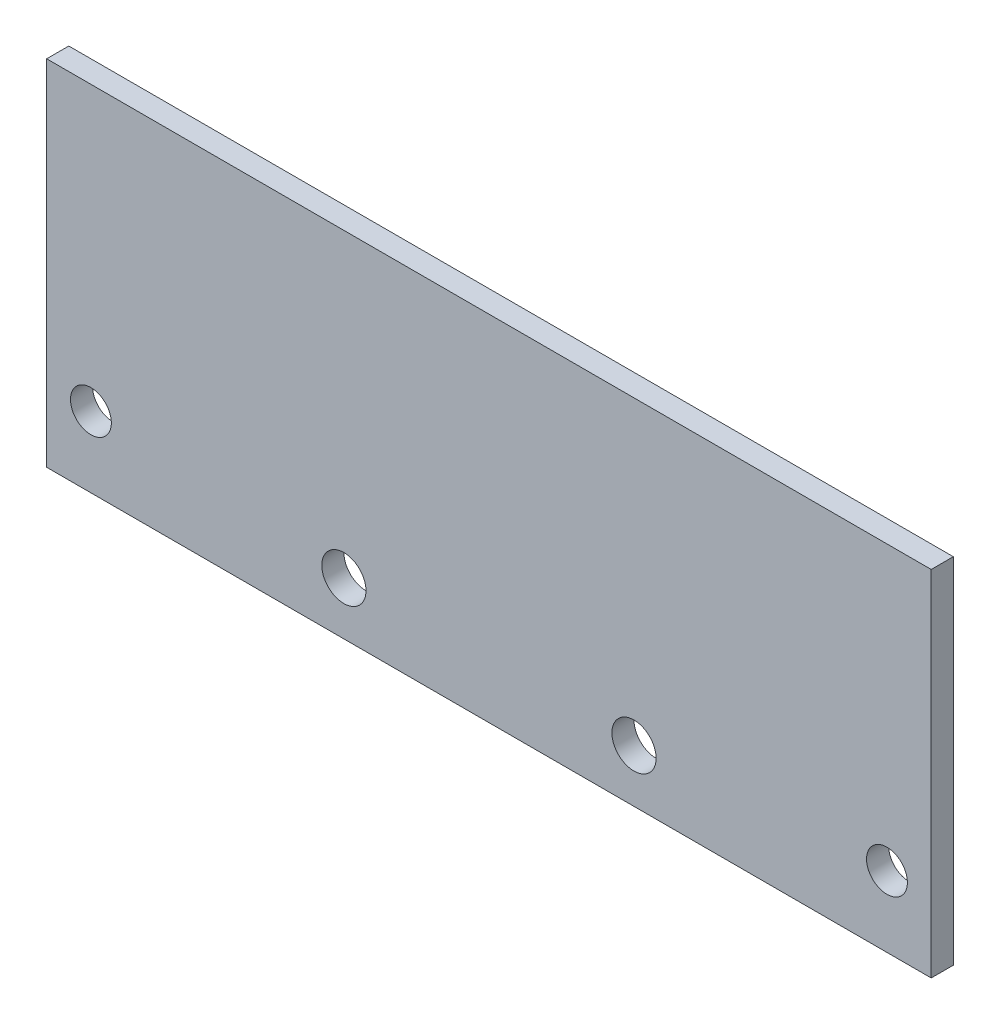
SolidWorks part; units mm, degrees
ref_plane "Front Plane" through (0, 0, 0) normal (0, 0, 1) x (1, 0, 0)
ref_plane "Top Plane" through (0, 0, 0) normal (0, 1, 0) x (1, 0, 0)
ref_plane "Right Plane" through (0, 0, 0) normal (1, 0, 0) x (0, 0, -1)
sketch "Sketch1" plane through (0, 0, 0) normal (0, 0, 1) x (1, 0, 0)
  line L1 (-63.5, 0) -> (63.5, 0)
  line L2 (-63.5, 0) -> (-63.5, 50.8)
  line L3 (-63.5, 50.8) -> (63.5, 50.8)
  line L4 (63.5, 0) -> (63.5, 50.8)
  point P6 (0, 0)
  dimension "D1" = 127
  dimension "D2" = 50.8
extrude "Boss-Extrude1" add sketch "Sketch1" along normal blind 3.175
sketch "Sketch2" plane through (0, 0, 0) normal (0, 0, -1) x (-1, 0, 0)
  circle A0 centre (-57.15, 10.16) radius 2.9337
  circle A1 centre (57.15, 10.16) radius 2.9337
  circle A2 centre (57.15, 10.16) radius 2.9337 construction
  circle A3 centre (20.828, 7.5674) radius 3.175
  circle A4 centre (-20.828, 7.5674) radius 3.175
  dimension "D1" = 6.35
extrude "Cut-Extrude1" cut sketch "Sketch2" against normal through all
